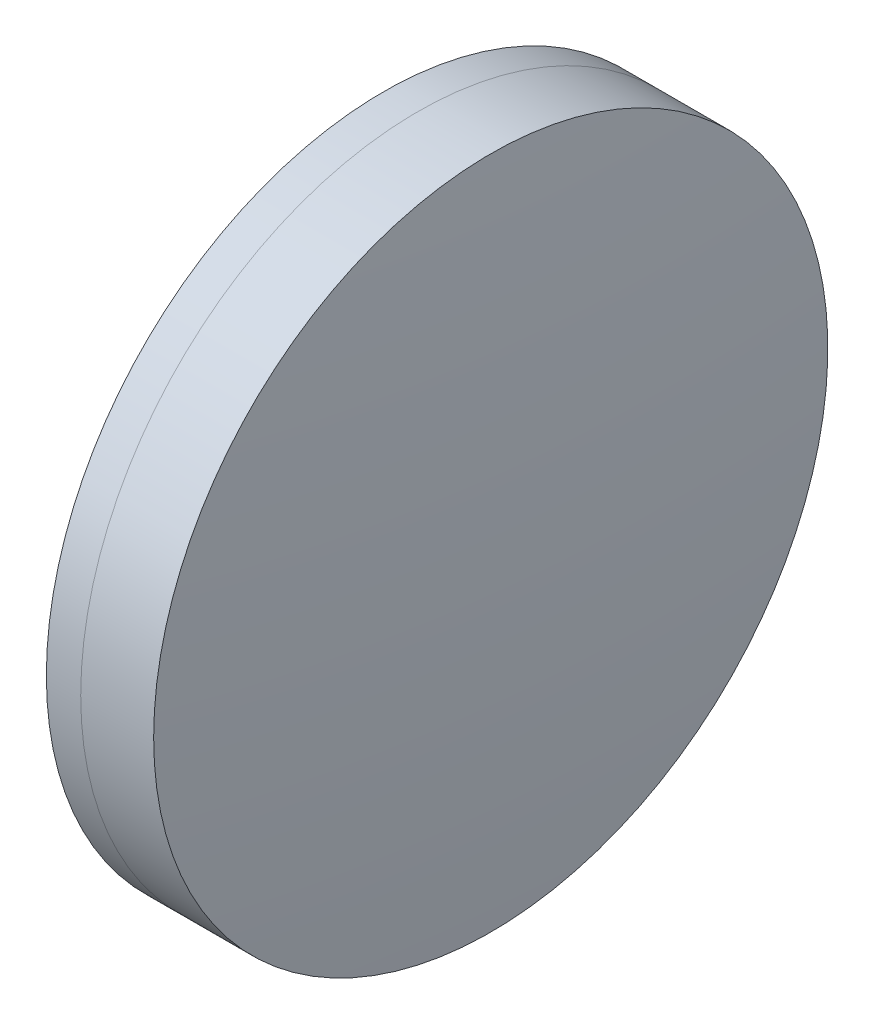
SolidWorks part; units mm, degrees
ref_plane "前视基准面" through (0, 0, 0) normal (0, 0, 1) x (1, 0, 0)
ref_plane "上视基准面" through (0, 0, 0) normal (0, 1, 0) x (1, 0, 0)
ref_plane "右视基准面" through (0, 0, 0) normal (1, 0, 0) x (0, 0, -1)
sketch "草图1" plane through (0, 0, 0) normal (0, 1, 0) x (1, 0, 0)
  line L0 (124.5233, 0) -> (395.1269, 0) construction
  line L1 (280.8784, -20) -> (282.9166, -20)
  line L2 (280.8784, 20) -> (282.9166, 20)
  arc A0 (282.9166, -20) -> (282.9166, 20) centre (210.1355, 0) ccw
  arc A1 (280.8784, 20) -> (280.8784, -20) centre (379.6835, 0) ccw
  point P10 (278.8745, 0)
  point P11 (285.6145, 0)
  dimension "D3" = 100.809
  dimension "D4" = 75.479
  dimension "D1" = 20
  dimension "D2" = 20
  dimension "D5" = 6.74
revolve "旋转1" add sketch "草图1" angle 360 about L0
sketch "草图2" plane through (0, 0, 0) normal (0, 1, 0) x (1, 0, 0)
  line L0 (-0.5519, 0) -> (409.4962, 0) construction
  line L2 (282.9166, 20) -> (287.2444, 20)
  line L3 (282.9166, -20) -> (287.2444, -20)
  arc A0 (287.2444, -20) -> (287.2444, 20) centre (57.8235, 0) ccw
  arc A1 (282.9166, -20) -> (282.9166, 20) centre (210.1355, 0) ccw construction
  arc A2 (282.9166, -20) -> (282.9166, 20) centre (210.1355, 0) ccw
  point P4 (285.6145, 0)
  point P8 (288.1145, 0)
  dimension "D1" = 230.291
  dimension "D2" = 2.5
revolve "旋转3" add sketch "草图2" angle 360 about L0
